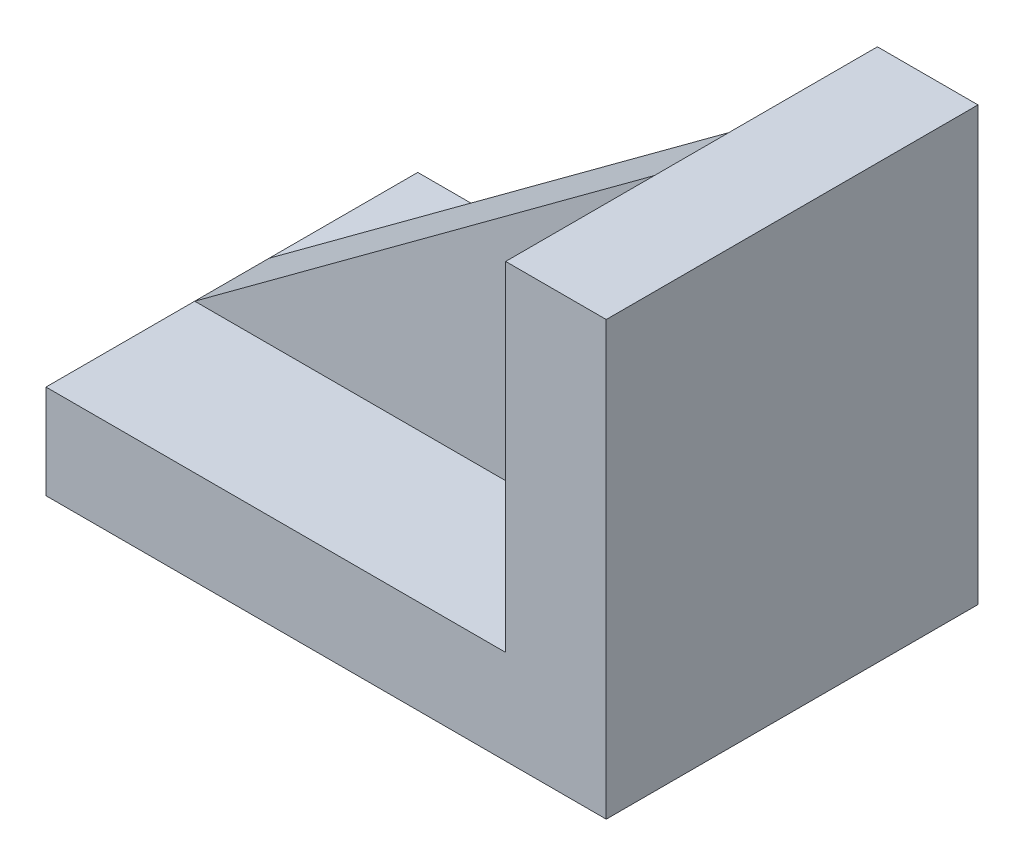
SolidWorks part; units mm, degrees
ref_plane "Front Plane" through (0, 0, 0) normal (0, 0, 1) x (1, 0, 0)
ref_plane "Top Plane" through (0, 0, 0) normal (0, 1, 0) x (1, 0, 0)
ref_plane "Right Plane" through (0, 0, 0) normal (1, 0, 0) x (0, 0, -1)
sketch "Sketch1" plane through (0, 0, 0) normal (0, 0, 1) x (1, 0, 0)
  line L1 (0, 0) -> (-61.8202, 0)
  line L3 (0, -12.6629) -> (-61.8202, -12.6629)
  line L4 (-61.8202, 0) -> (-61.8202, -12.6629)
  line L5 (0, -12.6629) -> (13.5281, -12.6629)
  line L6 (0, 0) -> (0, 45.5393)
  line L7 (0, 45.5393) -> (13.5281, 45.5393)
  line L8 (13.5281, -12.6629) -> (13.5281, 45.5393)
extrude "Boss-Extrude2" add sketch "Sketch1" along normal mid plane 50 contours L6 L7 L8 L5 L3 L4 L1
sketch "Sketch2" plane through (0, 0, 0) normal (0, 0, 1) x (1, 0, 0)
  line L0 (0, 45.5393) -> (-61.8202, 0)
rib "Rib4" sketch "Sketch2" sketch "Sketch2" thickness 10 extrusion direction parallel to sketch draft on no parameters "D1"=10
